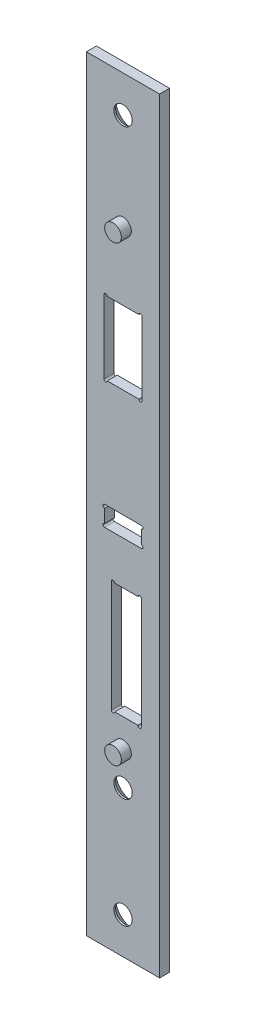
SolidWorks part; units mm, degrees
ref_plane "Face" through (0, 0, 0) normal (0, 0, 1) x (1, 0, 0)
ref_plane "Dessus" through (0, 0, 0) normal (0, 1, 0) x (1, 0, 0)
ref_plane "Droite" through (0, 0, 0) normal (1, 0, 0) x (0, 0, -1)
sketch "Esquisse1" plane through (0, 0, 0) normal (0, 0, 1) x (1, 0, 0)
  line L0 (0, 0) -> (-61.9891, 0) construction
  line L1 (-11, 115) -> (11, 115)
  line L2 (-11, 115) -> (-11, -115)
  line L3 (-11, -115) -> (11, -115)
  line L4 (11, 115) -> (11, -115)
  line L5 (-61.9891, 0) -> (0, 0) construction
  line L6 (0, 0) -> (0, -71.1874) construction
  dimension "D1" = 22
  dimension "D2" = 230
extrude "Extrusion1" add sketch "Esquisse1" along normal mid plane 3
hole_wizard "Diamètre du perçage Ø0.3 (0.3)1" positions "Esquisse3" profile "Esquisse5" hole size "Ø0.3" standard "ISO"
sketch "Esquisse3" plane through (0, 0, 1.5) normal (0, 0, 1) x (1, 0, 0)
  line L0 (11, 115) -> (-11, 115) construction
  line L1 (11, -115) -> (11, 115) construction
  point P0 (0, 104)
  point P7 (0, -71)
  point P10 (0, -104)
  dimension "D1" = 11
  dimension "D2" = 11
  dimension "D3" = 208
  dimension "D4" = 33
sketch "Esquisse5" plane through (0, 104, 1.5) normal (1, 0, 0) x (0, -1, 0)
  line L0 (0, 0) -> (0, 3.0901)
  line L1 (0, 3.0901) -> (0.15, 3)
  line L2 (0.15, 3) -> (0.15, 0)
  line L5 (0.15, 0) -> (0, 0)
  line L10 (0, 3.0901) -> (-0.15, 3) construction
  line L11 (0, -6.35) -> (0, 107.95) construction
  dimension "Diamètre du perçage" = 0.3
  dimension "Profondeur du perçage" = 3
  dimension "Angle de pointe" = 118
sketch "Esquisse7" plane through (0, 0, 1.5) normal (0, 0, 1) x (1, 0, 0)
  line L0 (0, 0) -> (0, 30.0857) construction
  line L1 (-4.75, 54.5) -> (4.75, 54.5)
  line L2 (-5.75, 54.5) -> (-5.75, 32.5)
  line L3 (-4.75, 32.5) -> (4.75, 32.5)
  line L4 (5.75, 54.5) -> (5.75, 32.5)
  arc A0 (-4.75, 54.5) -> (-5.75, 54.5) centre (-5.25, 54.5) ccw
  arc A1 (5.75, 54.5) -> (4.75, 54.5) centre (5.25, 54.5) ccw
  arc A2 (-5.75, 32.5) -> (-4.75, 32.5) centre (-5.25, 32.5) ccw
  arc A3 (5.75, 32.5) -> (4.75, 32.5) centre (5.25, 32.5) cw
  dimension "D4" = 1
  dimension "D5" = 1
  dimension "D7" = 1
  dimension "D1" = 11.5
  dimension "D2" = 22
  dimension "D3" = 32.5
extrude "Enlèv. mat.-Extru.1" cut sketch "Esquisse7" against normal up to next
sketch "Esquisse8" plane through (0, 0, 1.5) normal (0, 0, 1) x (1, 0, 0)
  line L0 (0, 0) -> (0, 20.99) construction
  line L1 (-5.5, 0) -> (5.5, 0)
  line L2 (-5.5, -1) -> (-5.5, -5)
  line L3 (-5.5, -6) -> (5.5, -6)
  line L4 (5.5, -1) -> (5.5, -5)
  line L5 (11, 115) -> (-11, 115) construction
  line L6 (11, -115) -> (11, 115) construction
  line L7 (0, 0) -> (0, -29.4953) construction
  arc A0 (-5.5, 0) -> (-5.5, -1) centre (-5.5, -0.5) ccw
  arc A1 (-5.5, -5) -> (-5.5, -6) centre (-5.5, -5.5) ccw
  arc A2 (5.5, 0) -> (5.5, -1) centre (5.5, -0.5) cw
  arc A3 (5.5, -5) -> (5.5, -6) centre (5.5, -5.5) cw
  dimension "D3" = 1
  dimension "D4" = 1
  dimension "D1" = 11
  dimension "D2" = 6
  dimension "D5" = 115
  dimension "D6" = 5.5
  dimension "D7" = 11
extrude "Enlèv. mat.-Extru.2" cut sketch "Esquisse8" against normal up to next
sketch "Esquisse9" plane through (0, 0, 1.5) normal (0, 0, 1) x (1, 0, 0)
  line L0 (1, 0) -> (1, -46.0339) construction
  line L1 (-2.5, -19) -> (4.5, -19)
  line L2 (-3.5, -19) -> (-3.5, -52.5)
  line L3 (-2.5, -52.5) -> (4.5, -52.5)
  line L4 (5.5, -19) -> (5.5, -52.5)
  line L5 (11, 115) -> (-11, 115) construction
  line L6 (11, -115) -> (11, 115) construction
  line L8 (-11, -115) -> (11, -115) construction
  arc A0 (-2.5, -19) -> (-3.5, -19) centre (-3, -19) ccw
  arc A1 (5.5, -52.5) -> (4.5, -52.5) centre (5, -52.5) cw
  arc A2 (-3.5, -52.5) -> (-2.5, -52.5) centre (-3, -52.5) ccw
  arc A3 (4.5, -19) -> (5.5, -19) centre (5, -19) cw
  dimension "D4" = 1
  dimension "D5" = 10
  dimension "D6" = 1
  dimension "D7" = 0.5
  dimension "D1" = 9
  dimension "D2" = 33.5
  dimension "D3" = 134
extrude "Enlèv. mat.-Extru.3" cut sketch "Esquisse9" against normal up to next
sketch "Esquisse10" plane through (0, 0, 1.5) normal (0, 0, 1) x (1, 0, 0)
  line L0 (11, -115) -> (11, 115) construction
  line L1 (11, 115) -> (-11, 115) construction
  line L3 (0, 0) -> (0, -123.6653) construction
  line L5 (5.5, 0) -> (-5.5, 0) construction
  line L6 (0, 0) -> (0, 7.7599) construction
  circle A0 centre (0, 75) radius 2.5
  circle A1 centre (0, -61) radius 2.5
  dimension "D1" = 5
  dimension "D4" = 5
  dimension "D2" = 11
  dimension "D3" = 40
  dimension "D5" = 136
extrude "Extrusion2" add sketch "Esquisse10" along normal blind 3
hole_wizard "Fraisage pour vis à tête fraisée M52" positions "Esquisse3D1" profile "Esquisse11" countersink size "M5" standard "ISO" end condition through all
sketch3d "Esquisse3D1"
  line L0 (0, -71, -1.5) -> (0, -71, 1.5) construction
  line L1 (0, -104, -1.5) -> (0, -104, 1.5) construction
  line L2 (0, 104, -1.5) -> (0, 104, 1.5) construction
  point P0 (0, -71, -1.5)
  point P4 (0, -104, -1.5)
  point P8 (0, 104, -1.5)
sketch "Esquisse11" plane through (0, -71, -1.5) normal (1, 0, 0) x (0, 1, 0)
  line L0 (0, 0) -> (0, 6)
  line L1 (0, 6) -> (2.75, 6)
  line L2 (2.75, 6) -> (2.75, 2.45)
  line L3 (2.75, 2.45) -> (5.2, 0)
  line L5 (5.2, 0) -> (0, 0)
  line L6 (-2.75, 2.45) -> (-5.2, 0) construction
  line L11 (0, -6.35) -> (0, 107.95) construction
  dimension "Diamètre du perçage jusqu'au prochain" = 5.5
  dimension "Profondeur du perçage jusqu'au prochain" = 6
  dimension "Diamètre du fraisage entrant" = 10.4
  dimension "Angle du fraisage entrant" = 90
